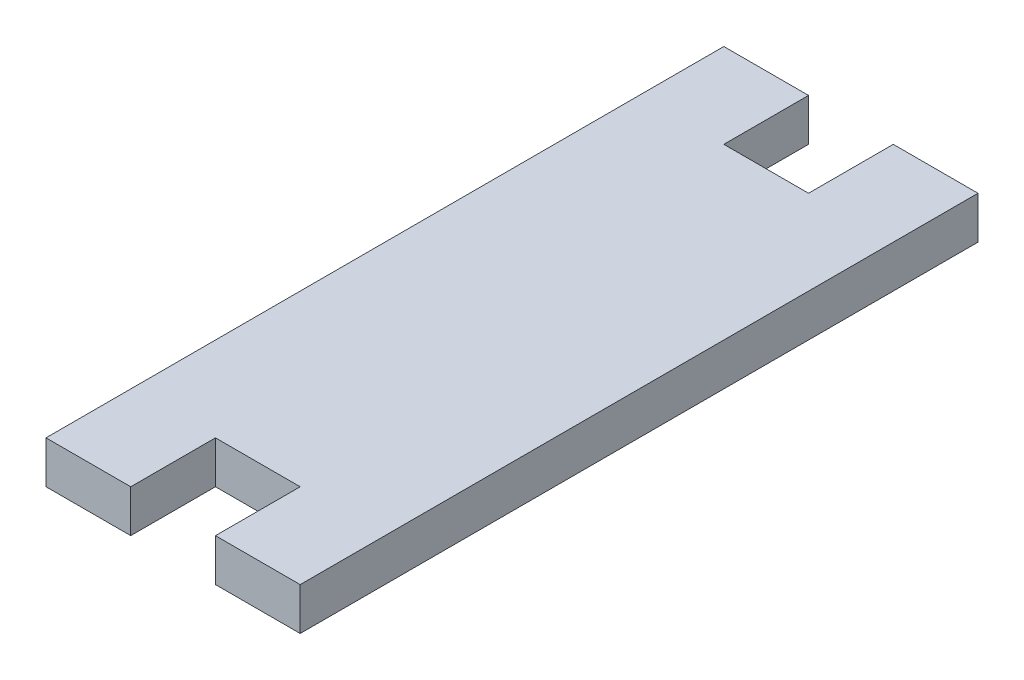
SolidWorks part; units mm, degrees
material "PMMA"
ref_plane "Front Plane" through (0, 0, 0) normal (0, 0, 1) x (1, 0, 0)
ref_plane "Top Plane" through (0, 0, 0) normal (0, 1, 0) x (1, 0, 0)
ref_plane "Right Plane" through (0, 0, 0) normal (1, 0, 0) x (0, 0, -1)
sketch "Schizzo1" plane through (0, 0, 0) normal (0, 1, 0) x (1, 0, 0)
  line L1 (-39.9699, 34.6914) -> (-9.9699, 34.6914)
  line L2 (-39.9699, 34.6914) -> (-39.9699, -45.3086)
  line L3 (-39.9699, -45.3086) -> (-9.9699, -45.3086)
  line L4 (-9.9699, 34.6914) -> (-9.9699, -45.3086)
  dimension "D1" = 80
  dimension "D2" = 30
extrude "Estrusione-Estrusione1" add sketch "Schizzo1" along normal blind 5
sketch "Schizzo2" plane through (0, 0, 0) normal (0, 1, 0) x (1, 0, 0)
  line L0 (-9.9699, 34.6914) -> (-39.9699, 34.6914) construction
  line L1 (-29.9699, 34.6914) -> (-19.9699, 34.6914)
  line L2 (-29.9699, 34.6914) -> (-29.9699, 24.6914)
  line L3 (-29.9699, 24.6914) -> (-19.9699, 24.6914)
  line L4 (-19.9699, 34.6914) -> (-19.9699, 24.6914)
  line L5 (-39.9699, 34.6914) -> (-39.9699, -45.3086) construction
  line L6 (-39.9699, -5.3086) -> (-9.9699, -5.3086) construction
  line L7 (-9.9699, -45.3086) -> (-9.9699, 34.6914) construction
  line L8 (-29.9699, -45.3086) -> (-29.9699, -35.3086)
  line L9 (-29.9699, -45.3086) -> (-19.9699, -45.3086)
  line L10 (-19.9699, -45.3086) -> (-19.9699, -35.3086)
  line L11 (-29.9699, -35.3086) -> (-19.9699, -35.3086)
  dimension "D1" = 10
  dimension "D2" = 10
  dimension "D3" = 10
extrude "Taglio-Estrusione1" cut sketch "Schizzo2" along direction (0, 1, 0) on the side of the normal through all
equation "\"Thickness5\"=5"
equation "\"D1@Estrusione-Estrusione1\"=\"Thickness5\""
equation "\"BeltWidth\"=50"
equation "\"D3@Schizzo2\"=2*\"Thickness5\""
equation "\"Width\"= \"BeltWidth\" + 2 * \"Thickness5\""
